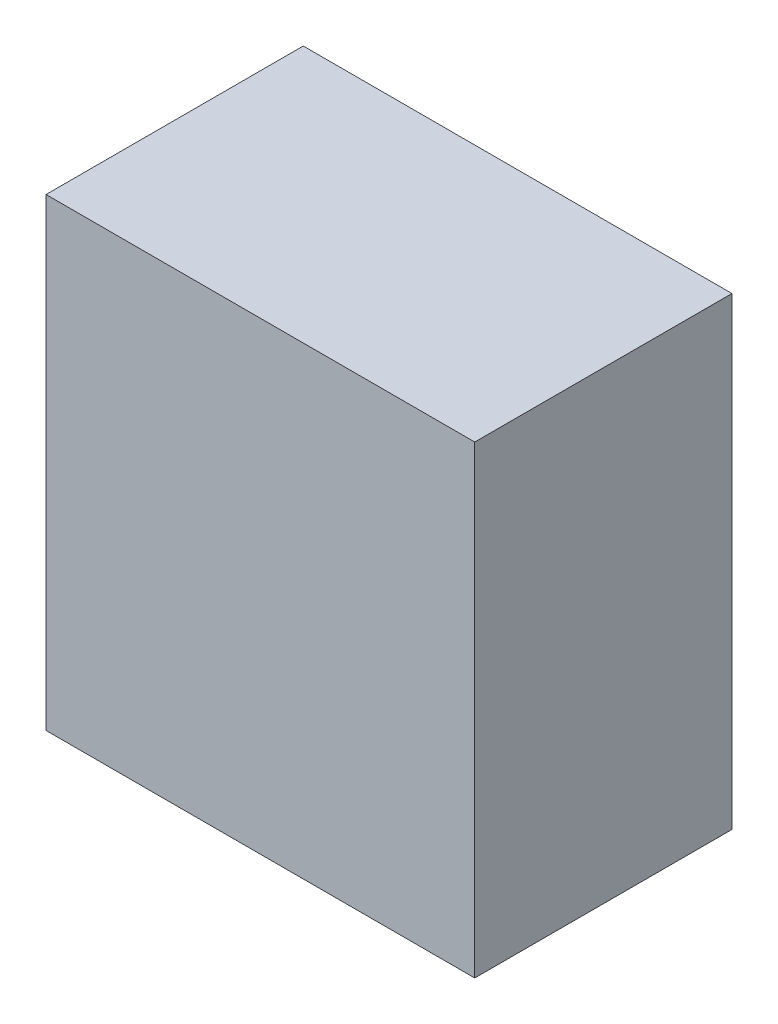
SolidWorks part; units mm, degrees
ref_plane "Front Plane" through (0, 0, 0) normal (0, 0, 1) x (1, 0, 0)
ref_plane "Top Plane" through (0, 0, 0) normal (0, 1, 0) x (1, 0, 0)
ref_plane "Right Plane" through (0, 0, 0) normal (1, 0, 0) x (0, 0, -1)
sketch "Sketch1" plane through (0, 0, 0) normal (0, 0, 1) x (1, 0, 0)
  line L1 (305, -55.73) -> (160, -55.73)
  line L2 (305, -55.73) -> (305, 101.27)
  line L3 (305, 101.27) -> (160, 101.27)
  line L4 (160, -55.73) -> (160, 101.27)
  dimension "D1" = 157
  dimension "D2" = 145
extrude "Boss-Extrude1" add sketch "Sketch1" along normal blind 87
